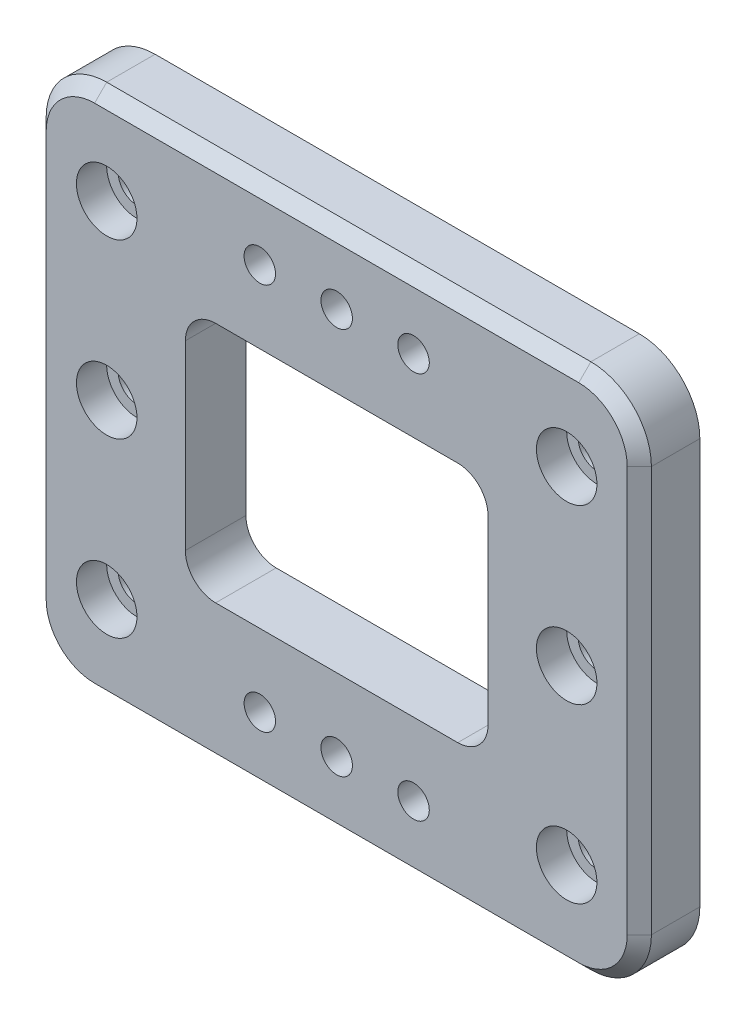
SolidWorks part; units mm, degrees
ref_plane "前视基准面" through (0, 0, 0) normal (0, 0, 1) x (1, 0, 0)
ref_plane "上视基准面" through (0, 0, 0) normal (0, 1, 0) x (1, 0, 0)
ref_plane "右视基准面" through (0, 0, 0) normal (1, 0, 0) x (0, 0, -1)
sketch "草图1" plane through (0, 0, 0) normal (0, 0, 1) x (1, 0, 0)
  line L1 (-50, 43.5) -> (50, 43.5)
  line L2 (-50, 43.5) -> (-50, -43.5)
  line L3 (-50, -43.5) -> (50, -43.5)
  line L4 (50, 43.5) -> (50, -43.5)
  line L5 (-50, 43.5) -> (50, -43.5) construction
  line L6 (-50, -43.5) -> (50, 43.5) construction
  point P0 (0, 0)
  dimension "D1" = 100
  dimension "D2" = 87
extrude "凸台-拉伸1" add sketch "草图1" along normal blind 10
fillet "圆角1" radius 10 4 edges at (50, -43.5, 5) (-50, -43.5, 5) (50, 43.5, 5) (-50, 43.5, 5)
sketch "草图2" plane through (0, 0, 10) normal (0, 0, 1) x (1, 0, 0)
  line L0 (0, 43.5) -> (0, 32) construction
  line L1 (40, 43.5) -> (-40, 43.5) construction
  line L2 (0, 32) -> (-12.7, 32) construction
  line L3 (0, 32) -> (0, -32) construction
  line L4 (0, -32) -> (-12.7, -32) construction
  line L5 (0, -32) -> (12.7, -32) construction
  circle A0 centre (0, 32) radius 2.6
  circle A1 centre (-12.7, 32) radius 2.6
  circle A2 centre (12.7, 32) radius 2.6
  circle A3 centre (-12.7, -32) radius 2.6
  circle A4 centre (0, -32) radius 2.6
  circle A5 centre (12.7, -32) radius 2.6
  point P16 (0, 0)
  dimension "D1" = 12.7
  dimension "D2" = 0
  dimension "D3" = 64
extrude "切除-拉伸1" cut sketch "草图2" against normal blind 10
sketch "草图3" plane through (0, 0, 10) normal (0, 0, 1) x (1, 0, 0)
  line L0 (-50, 0) -> (-38, 0) construction
  line L1 (-50, 33.5) -> (-50, -33.5) construction
  line L2 (-38, 0) -> (-38, 28.5) construction
  line L3 (-38, 0) -> (-38, -28.5) construction
  line L4 (0, 0) -> (0, 10) construction
  line L6 (-40, -43.5) -> (40, -43.5) construction
  line L7 (40, 43.5) -> (-40, 43.5) construction
  circle A0 centre (-38, 28.5) radius 5
  circle A1 centre (-38, 0) radius 5
  circle A2 centre (-38, -28.5) radius 5
  circle A3 centre (38, -28.5) radius 5
  circle A4 centre (38, 0) radius 5
  circle A5 centre (38, 28.5) radius 5
  dimension "D1" = 76
  dimension "D2" = 15
  dimension "D3" = 15
extrude "切除-拉伸2" cut sketch "草图3" against normal blind 5
sketch "草图4" plane through (0, 0, 5) normal (0, 0, 1) x (1, 0, 0)
  circle A0 centre (-38, 28.5) radius 3.1
  circle A1 centre (-38, 0) radius 3.1
  circle A2 centre (-38, -28.5) radius 3.1
  circle A3 centre (38, 28.5) radius 3.1
  circle A4 centre (38, 0) radius 3.1
  circle A5 centre (38, -28.5) radius 3.1
extrude "切除-拉伸3" cut sketch "草图4" against normal blind 5
chamfer "倒角1" distance 1 angle 45 6 edges at (41.1, 28.5, 0) (41.1, 0, 0) (41.1, -28.5, 0) (-34.9, -28.5, 0) (-34.9, 0, 0) (-34.9, 28.5, 0)
chamfer "倒角2" distance 2 angle 45 8 edges at (50, 0, 10) (47.0711, 40.5711, 10) (47.0711, -40.5711, 10) (0, 43.5, 10) (0, -43.5, 10) (-47.0711, 40.5711, 10) (-47.0711, -40.5711, 10) (-50, 0, 10)
sketch "Sketch1" plane through (0, 0, 10) normal (0, 0, 1) x (1, 0, 0)
  line L1 (-25, 20) -> (25, 20)
  line L2 (-25, 20) -> (-25, -20)
  line L3 (-25, -20) -> (25, -20)
  line L4 (25, 20) -> (25, -20)
  line L5 (-25, 20) -> (25, -20) construction
  line L6 (-25, -20) -> (25, 20) construction
  point P0 (0, 0)
  dimension "D1" = 40
  dimension "D2" = 50
extrude "Cut-Extrude1" cut sketch "Sketch1" against normal blind 10
fillet "Fillet1" radius 5 4 edges at (-25, -20, 5) (25, -20, 5) (25, 20, 5) (-25, 20, 5)
